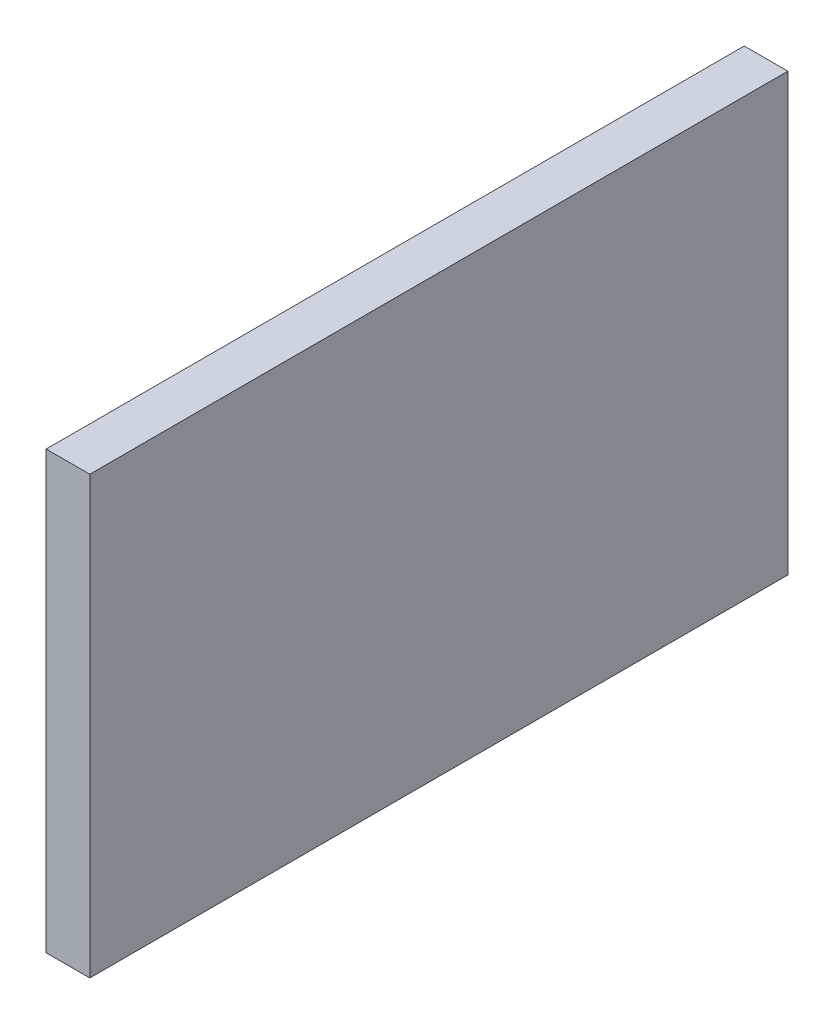
SolidWorks part; units mm, degrees
material "POLYURETHANE (11671)"
ref_plane "Front Plane" through (0, 0, 0) normal (0, 0, 1) x (1, 0, 0)
ref_plane "Top Plane" through (0, 0, 0) normal (0, 1, 0) x (1, 0, 0)
ref_plane "Right Plane" through (0, 0, 0) normal (1, 0, 0) x (0, 0, -1)
sketch "Sketch1" plane through (0, 0, 0) normal (1, 0, 0) x (0, 0, -1)
  line L1 (-25.4, -15.875) -> (25.4, -15.875)
  line L2 (-25.4, -15.875) -> (-25.4, 15.875)
  line L3 (-25.4, 15.875) -> (25.4, 15.875)
  line L4 (25.4, -15.875) -> (25.4, 15.875)
  line L5 (-25.4, -15.875) -> (25.4, 15.875) construction
  line L6 (-25.4, 15.875) -> (25.4, -15.875) construction
  point P0 (0, 0)
  dimension "D1" = 50.8
  dimension "D2" = 31.75
extrude "Boss-Extrude1" add sketch "Sketch1" along normal blind 3.175
